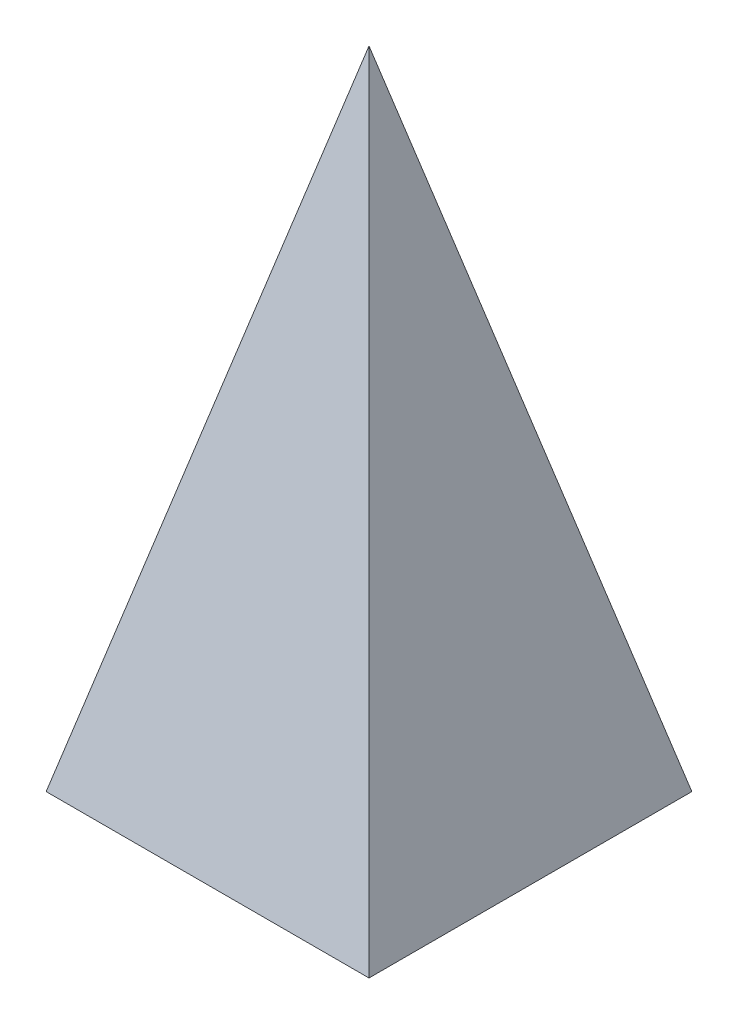
SolidWorks part; units mm, degrees
ref_plane "Front" through (0, 0, 0) normal (0, 0, 1) x (1, 0, 0)
ref_plane "Top" through (0, 0, 0) normal (0, 1, 0) x (1, 0, 0)
ref_plane "Right" through (0, 0, 0) normal (1, 0, 0) x (0, 0, -1)
sketch "Sketch1" plane through (0, 0, 0) normal (0, 1, 0) x (1, 0, 0)
  line L0 (5, 5) -> (-5, -5) construction
  line L1 (-5, 5) -> (5, 5)
  line L2 (-5, 5) -> (-5, -5)
  line L3 (-5, -5) -> (5, -5)
  line L4 (5, 5) -> (5, -5)
  dimension "D1" = 10
sketch "Sketch2" plane through (0, 0, 0) normal (0, 0, 1) x (1, 0, 0)
  point P0 (0, 20)
  dimension "D1" = 20
loft "Loft1" add profiles "Sketch2", "Sketch1"
